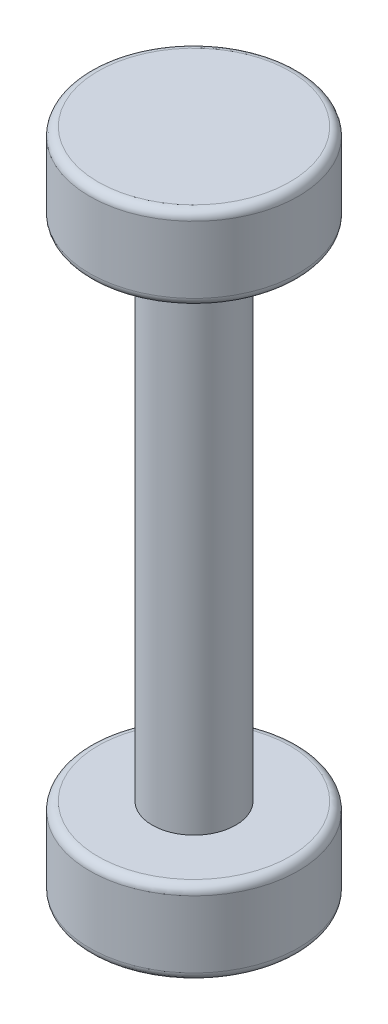
SolidWorks part; units mm, degrees
ref_plane "Front Plane" through (0, 0, 0) normal (0, 0, 1) x (1, 0, 0)
ref_plane "Top Plane" through (0, 0, 0) normal (0, 1, 0) x (1, 0, 0)
ref_plane "Right Plane" through (0, 0, 0) normal (1, 0, 0) x (0, 0, -1)
sketch "Sketch1" plane through (0, 0, 0) normal (0, 1, 0) x (1, 0, 0)
  circle A0 centre (0, 0) radius 2.5
  dimension "D1" = 5
extrude "Boss-Extrude1" add sketch "Sketch1" against normal blind 2 contours A0
sketch "Sketch2" plane through (0, -2, 0) normal (0, -1, 0) x (1, 0, 0)
  circle A0 centre (0, 0) radius 1
  dimension "D1" = 2
extrude "Boss-Extrude2" add sketch "Sketch2" along normal blind 12
sketch "Sketch3" plane through (0, -14, 0) normal (0, -1, 0) x (1, 0, 0)
  circle A0 centre (0, 0) radius 2.5 construction
  circle A1 centre (0, 0) radius 2.5
extrude "Boss-Extrude3" add sketch "Sketch3" along normal blind 2
fillet "Fillet1" radius 0.2 4 edges at (0, -14, -2.5) (0, -2, 2.5) (0, -16, -2.5) (0, 0, 2.5)
